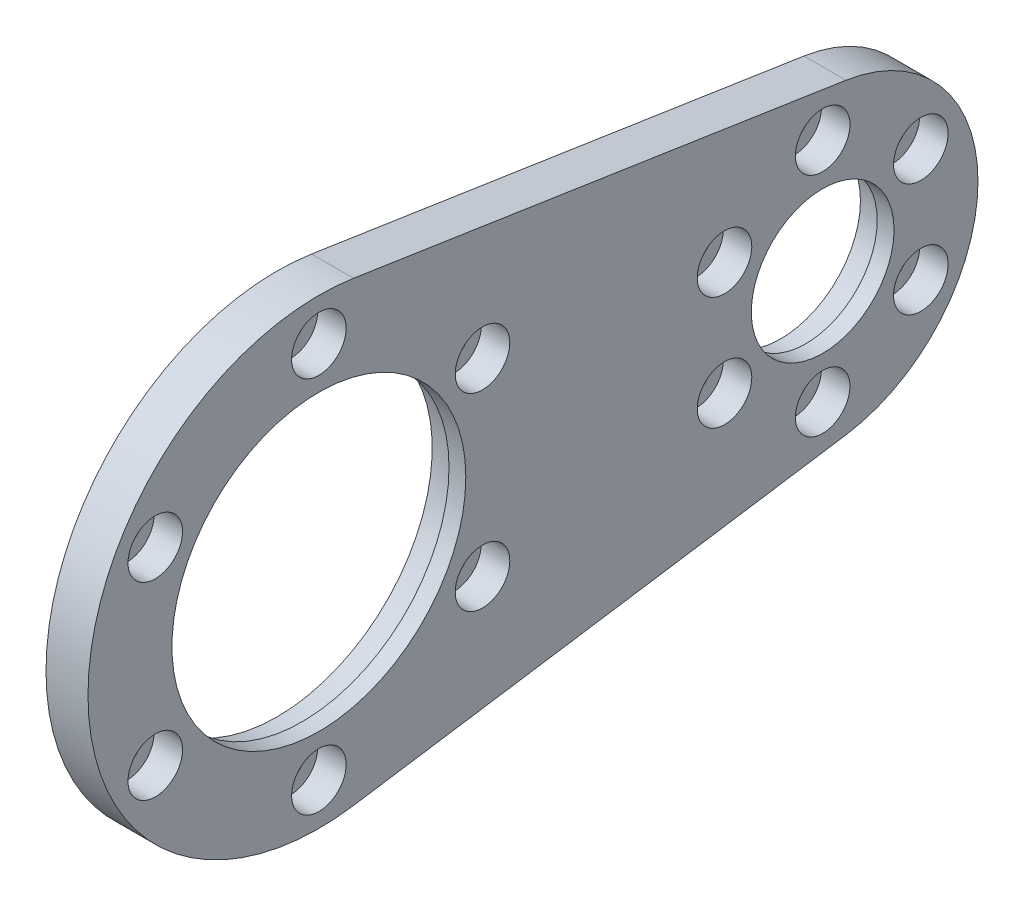
SolidWorks part; units mm, degrees
material "7075-T6 (SN)"
ref_plane "정면" through (0, 0, 0) normal (0, 0, 1) x (1, 0, 0)
ref_plane "윗면" through (0, 0, 0) normal (0, 1, 0) x (1, 0, 0)
ref_plane "우측면" through (0, 0, 0) normal (1, 0, 0) x (0, 0, -1)
sketch "스케치3" plane through (0, 0, 0) normal (1, 0, 0) x (0, 0, -1)
  circle A0 centre (0, 0) radius 27.5
  dimension "D1" = 55
extrude "보스-돌출1" add sketch "스케치3" along normal blind 2
sketch "스케치4" plane through (2, 0, 0) normal (1, 0, 0) x (0, 0, -1)
  circle A0 centre (0, 0) radius 17.5
  circle A1 centre (0, 0) radius 27.5
  circle A2 centre (0, 0) radius 27.5 construction
  dimension "D1" = 35
extrude "보스-돌출2" add sketch "스케치4" along normal blind 1
sketch "스케치5" plane through (3, 0, 0) normal (1, 0, 0) x (0, 0, -1)
  circle A0 centre (0, 0) radius 18.5
  circle A1 centre (0, 0) radius 27.5
  circle A2 centre (0, 0) radius 27.5 construction
  dimension "D1" = 37
extrude "보스-돌출3" add sketch "스케치5" along normal blind 7
sketch "스케치6" plane through (10, 0, 0) normal (1, 0, 0) x (0, 0, -1)
  circle A0 centre (0, 0) radius 27.5
  circle A1 centre (0, 0) radius 17.5
  circle A2 centre (0, 0) radius 27.5 construction
  dimension "D1" = 35
extrude "보스-돌출4" add sketch "스케치6" along normal blind 2
sketch "스케치10" plane through (12, 0, 0) normal (1, 0, 0) x (0, 0, -1)
  line L0 (0, 0) -> (60, 0) construction
  line L1 (4.125, 27.1889) -> (62.775, 18.2907)
  line L2 (4.125, -27.1889) -> (62.775, -18.2907)
  arc A0 (62.775, -18.2907) -> (62.775, 18.2907) centre (60, 0) ccw
  arc A1 (4.125, -27.1889) -> (4.125, 27.1889) centre (0, 0) ccw
  circle A2 centre (0, 0) radius 27.5 construction
  dimension "D1" = 37
  dimension "D2" = 60
extrude "보스-돌출5" add sketch "스케치10" against normal blind 9
ref_plane "평면2" through (7.5, 0, 0) normal (1, 0, 0) x (0, 0, -1)
sketch "스케치11" plane through (7.5, 0, 0) normal (1, 0, 0) x (0, 0, -1)
  circle A0 centre (60, 0) radius 8.5
  arc A1 (62.775, -18.2907) -> (62.775, 18.2907) centre (60, 0) ccw construction
  dimension "D1" = 17
extrude "컷-돌출3" cut sketch "스케치11" against normal mid plane 222
sketch "스케치12" plane through (7.5, 0, 0) normal (1, 0, 0) x (0, 0, -1)
  circle A0 centre (60, 0) radius 9.5
  circle A1 centre (60, 0) radius 8.5 construction
  dimension "D1" = 19
extrude "컷-돌출4" cut sketch "스케치12" against normal mid plane 5
sketch "스케치13" plane through (0, 0, 0) normal (-1, 0, 0) x (0, 0, 1)
  circle A0 centre (0, 0) radius 9.5
  circle A1 centre (0, 0) radius 27.5 construction
  dimension "D1" = 19
extrude "보스-돌출6" add sketch "스케치13" along normal blind 5
sketch "스케치14" plane through (2, 0, 0) normal (1, 0, 0) x (0, 0, -1)
  circle A0 centre (0, 0) radius 5 construction
  dimension "D1" = 10
hole_wizard "M3 육각 소켓 머리 캡 나사용 카운터보어4" positions "스케치15" profile "스케치16" counterbore size "M3" standard "ISO" end condition through all
sketch "스케치15" plane through (2, 0, 0) normal (1, 0, 0) x (0, 0, -1)
  circle A0 centre (0, 0) radius 5 construction
  point P0 (0, 5)
sketch "스케치16" plane through (2, 5, 0) normal (0, 1, 0) x (0, 0, -1)
  line L0 (0, 0) -> (0, 7)
  line L1 (0, 7) -> (1.7, 7)
  line L3 (1.7, 7) -> (1.7, 3.4)
  line L4 (1.7, 3.4) -> (3.25, 3.4)
  line L5 (3.25, 3.4) -> (3.25, 0)
  line L7 (3.25, 0) -> (0, 0)
  line L11 (0, -6.35) -> (0, 107.95) construction
  dimension "관통 구멍 지름" = 3.4
  dimension "관통 구멍 깊이" = 7
  dimension "카운터보어 지름" = 6.5
  dimension "카운터보어 깊이" = 3.4
pattern_circular "원형 패턴1" count 3 over 360 about axis through (0, 0, 0) along (1, 0, 0) of "M3 육각 소켓 머리 캡 나사용 카운터보어4"
sketch "스케치17" plane through (0, 0, 0) normal (0, 0, 1) x (1, 0, 0)
  line L0 (12, -27.5) -> (12, 27.5) construction
  line L1 (7, 30.4497) -> (-18.0347, 30.4497)
  line L2 (7, 30.4497) -> (7, -34.1546)
  line L3 (7, -34.1546) -> (-18.0347, -34.1546)
  line L4 (-18.0347, 30.4497) -> (-18.0347, -34.1546)
  dimension "D1" = 5
extrude "컷-돌출5" cut sketch "스케치17" against normal mid plane 2222
sketch "스케치18" plane through (12, 0, 0) normal (1, 0, 0) x (0, 0, -1)
  circle A0 centre (0, 0) radius 22.5 construction
  circle A1 centre (0, 0) radius 17.5 construction
  dimension "D1" = 45
hole_wizard "M3 육각 소켓 머리 캡 나사용 카운터보어2" positions "스케치22" profile "스케치23" counterbore size "M3" standard "ISO" end condition through all
sketch "스케치22" plane through (12, 0, 0) normal (1, 0, 0) x (0, 0, -1)
  circle A0 centre (0, 0) radius 22.5 construction
  point P0 (0, 22.5)
sketch "스케치23" plane through (12, 22.5, 0) normal (0, 1, 0) x (0, 0, -1)
  line L0 (0, 0) -> (0, 5)
  line L1 (0, 5) -> (1.6, 5)
  line L3 (1.6, 5) -> (1.6, 3.4)
  line L4 (1.6, 3.4) -> (3.25, 3.4)
  line L5 (3.25, 3.4) -> (3.25, 0)
  line L7 (3.25, 0) -> (0, 0)
  line L11 (0, -6.35) -> (0, 107.95) construction
  dimension "관통 구멍 지름" = 3.2
  dimension "관통 구멍 깊이" = 5
  dimension "카운터보어 지름" = 6.5
  dimension "카운터보어 깊이" = 3.4
pattern_circular "원형 패턴2" count 6 over 360 about axis through (0, 0, 0) along (1, 0, 0) of "M3 육각 소켓 머리 캡 나사용 카운터보어2"
sketch "스케치25" plane through (12, 0, 0) normal (1, 0, 0) x (0, 0, -1)
  circle A0 centre (60, 0) radius 13.5 construction
  circle A1 centre (60, 0) radius 8.5 construction
  dimension "D1" = 27
hole_wizard "M3 육각 소켓 머리 캡 나사용 카운터보어3" positions "스케치26" profile "스케치27" counterbore size "M3" standard "ISO" end condition through all
sketch "스케치26" plane through (12, 0, 0) normal (1, 0, 0) x (0, 0, -1)
  circle A0 centre (60, 0) radius 13.5 construction
  point P0 (60, 13.5)
sketch "스케치27" plane through (12, 13.5, -60) normal (0, 1, 0) x (0, 0, -1)
  line L0 (0, 0) -> (0, 5)
  line L1 (0, 5) -> (1.6, 5)
  line L3 (1.6, 5) -> (1.6, 3.4)
  line L4 (1.6, 3.4) -> (3.25, 3.4)
  line L5 (3.25, 3.4) -> (3.25, 0)
  line L7 (3.25, 0) -> (0, 0)
  line L11 (0, -6.35) -> (0, 107.95) construction
  dimension "관통 구멍 지름" = 3.2
  dimension "관통 구멍 깊이" = 5
  dimension "카운터보어 지름" = 6.5
  dimension "카운터보어 깊이" = 3.4
pattern_circular "원형 패턴3" count 6 over 360 about axis through (0, 0, -60) along (1, 0, 0) of "M3 육각 소켓 머리 캡 나사용 카운터보어3"
